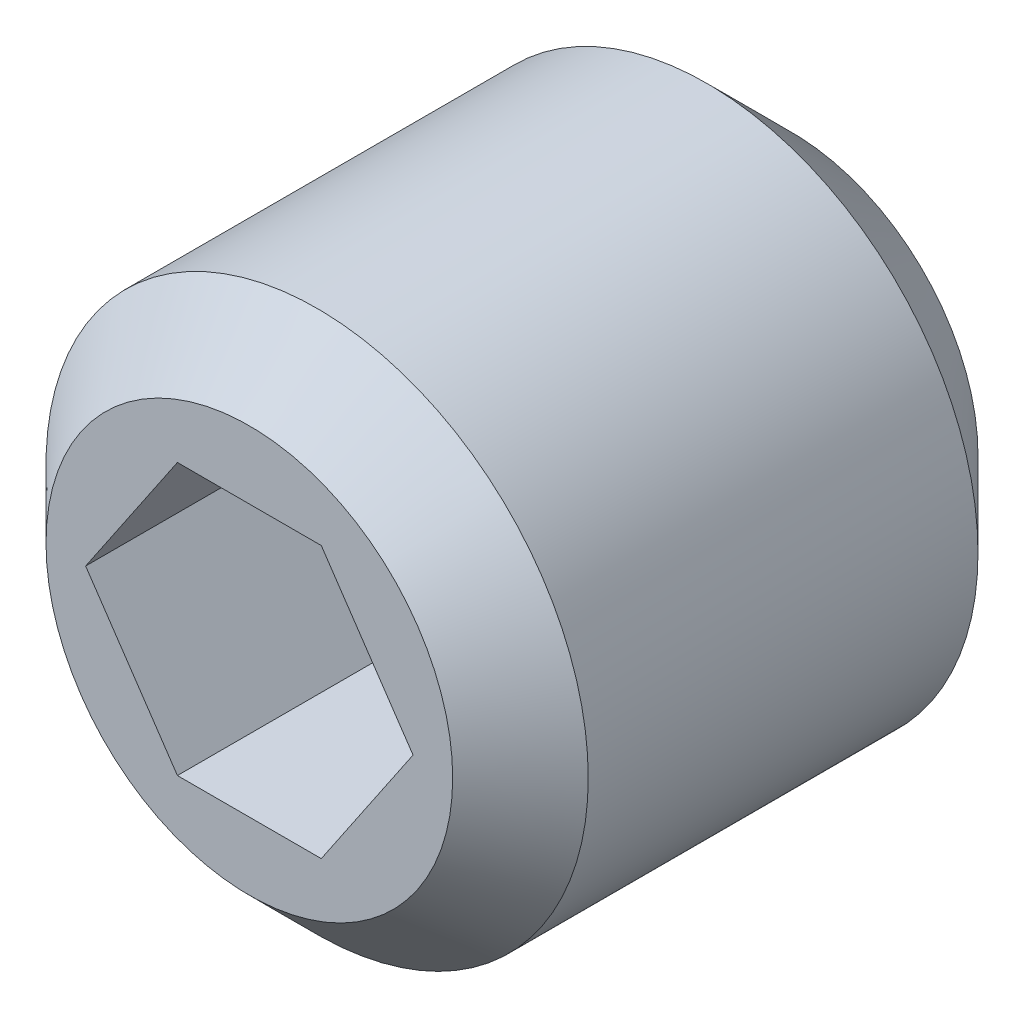
SolidWorks part; units mm, degrees
ref_plane "Plane1" through (0, 0, 0) normal (0, 0, 1) x (1, 0, 0)
ref_plane "Plane2" through (0, 0, 0) normal (0, 1, 0) x (1, 0, 0)
ref_plane "Plane3" through (0, 0, 0) normal (1, 0, 0) x (0, 0, -1)
sketch "Esquisse1" plane through (0, 0, 0) normal (0, 0, 1) x (1, 0, 0)
  circle A0 centre (0, 0) radius 4
  dimension "D1" = 8
extrude "Base-Extrusion" add sketch "Esquisse1" along normal blind 8
chamfer "Chanfrein1" distance 1.25 angle 45
sketch "Esquisse2" plane through (0, 0, 8) normal (0, 0, 1) x (1, 0, 0)
  line L0 (0, 0) -> (2.5826, 0) construction
  line L1 (0, 0) -> (0, 1.8876) construction
  line L2 (2.4152, 0) -> (1.0613, 2)
  line L3 (1.0613, 2) -> (-1.0613, 2)
  line L4 (-1.0613, 2) -> (-2.4152, 0)
  line L5 (-2.4152, 0) -> (-1.0613, -2)
  line L6 (-1.0613, -2) -> (1.0613, -2)
  line L7 (1.0613, -2) -> (2.4152, 0)
  dimension "D1" = 4
  dimension "D2" = 4
extrude "Enlèv. mat.-Extru.1" cut sketch "Esquisse2" against normal blind 4
chamfer "Chanfrein2" distance 1 angle 45
